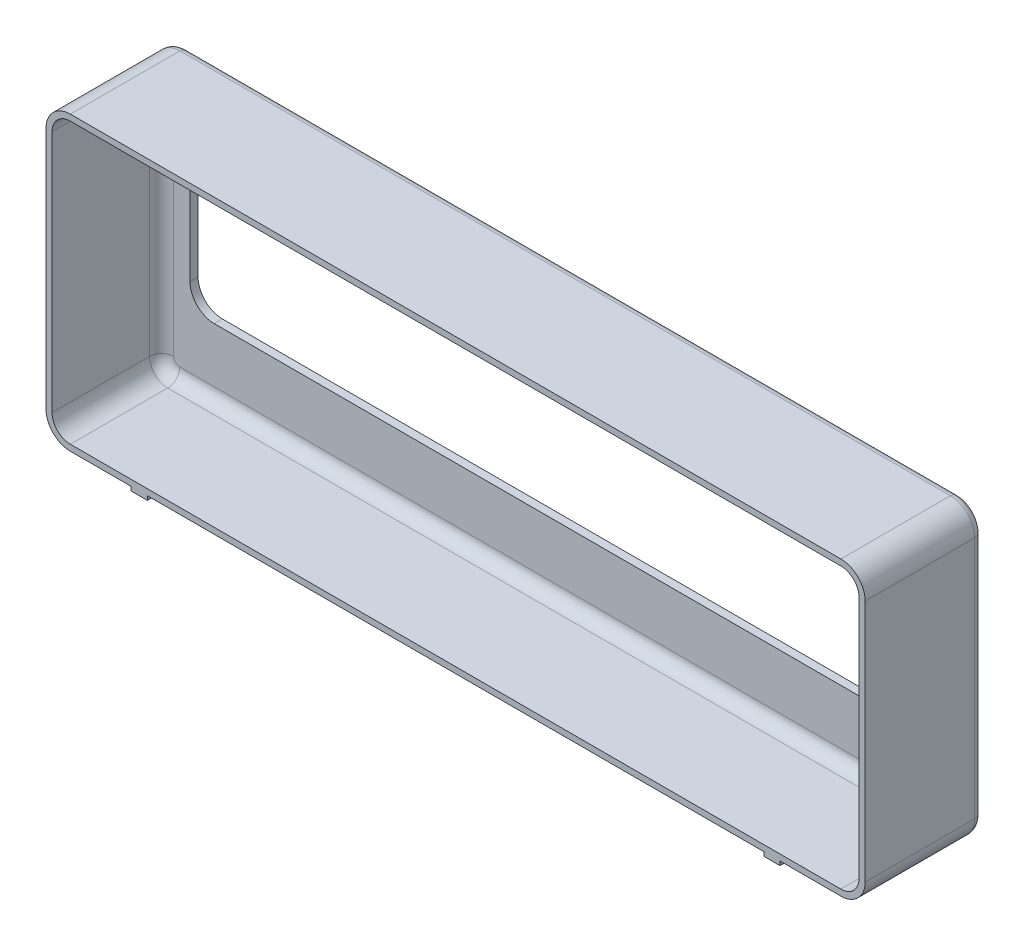
SolidWorks part; units mm, degrees
ref_plane "Front Plane" through (0, 0, 0) normal (0, 0, 1) x (1, 0, 0)
ref_plane "Top Plane" through (0, 0, 0) normal (0, 1, 0) x (1, 0, 0)
ref_plane "Right Plane" through (0, 0, 0) normal (1, 0, 0) x (0, 0, -1)
sketch "Sketch1" plane through (0, 0, 0) normal (0, 0, 1) x (1, 0, 0)
  line L1 (0, 0) -> (202, 0)
  line L2 (0, 0) -> (0, 72)
  line L3 (0, 72) -> (202, 72)
  line L4 (202, 0) -> (202, 72)
  dimension "D1" = 72
  dimension "D2" = 202
extrude "Boss-Extrude1" add sketch "Sketch1" along normal blind 29
sketch "Sketch2" plane through (0, 0, 29) normal (0, 0, 1) x (1, 0, 0)
  line L0 (202, 72) -> (0, 72) construction
  line L1 (1.5, 70.5) -> (200.5, 70.5)
  line L2 (1.5, 70.5) -> (1.5, 1.5)
  line L3 (1.5, 1.5) -> (200.5, 1.5)
  line L4 (200.5, 70.5) -> (200.5, 1.5)
  line L5 (0, 72) -> (0, 0) construction
  line L6 (0, 0) -> (202, 0) construction
  line L7 (202, 0) -> (202, 72) construction
  dimension "D1" = 1.5
  dimension "D2" = 1.5
  dimension "D3" = 1.5
  dimension "D4" = 1.5
extrude "Cut-Extrude1" cut sketch "Sketch2" against normal blind 27
sketch "Sketch3" plane through (0, 0, 2) normal (0, 0, 1) x (1, 0, 0)
  line L0 (200.5, 70.5) -> (1.5, 70.5) construction
  line L1 (8.5, 55) -> (193.5, 55)
  line L2 (8.5, 55) -> (8.5, 18)
  line L3 (8.5, 18) -> (193.5, 18)
  line L4 (193.5, 55) -> (193.5, 18)
  line L5 (1.5, 1.5) -> (200.5, 1.5) construction
  line L6 (1.5, 70.5) -> (1.5, 1.5) construction
  line L7 (200.5, 1.5) -> (200.5, 70.5) construction
  dimension "D1" = 15.5
  dimension "D2" = 16.5
  dimension "D3" = 7
  dimension "D4" = 7
extrude "Cut-Extrude2" cut sketch "Sketch3" against normal blind 27
fillet "Fillet1" radius 6 4 edges at (193.5, 18, 1) (193.5, 55, 1) (8.5, 18, 1) (8.5, 55, 1)
fillet "Fillet2" radius 4.5 4 edges at (200.5, 70.5, 15.5) (200.5, 1.5, 15.5) (1.5, 1.5, 15.5) (1.5, 70.5, 15.5)
fillet "Fillet3" radius 6 4 edges at (202, 0, 14.5) (202, 72, 14.5) (0, 0, 14.5) (0, 72, 14.5)
sketch "Sketch4" plane through (0, 0, 0) normal (0, -1, 0) x (-1, 0, 0)
  line L0 (-6, -29) -> (-196, -29) construction
  line L1 (-21, -29) -> (-25, -29)
  line L2 (-21, -29) -> (-21, 0)
  line L3 (-21, 0) -> (-25, 0)
  line L4 (-25, -29) -> (-25, 0)
  line L5 (-6, 0) -> (-196, 0) construction
  line L6 (-181, -29) -> (-177, -29)
  line L7 (-181, -29) -> (-181, 0)
  line L8 (-181, 0) -> (-177, 0)
  line L9 (-177, -29) -> (-177, 0)
  line L10 (-6, -29) -> (-6, 0) construction
  line L11 (-196, 0) -> (-196, -29) construction
  dimension "D1" = 15
  dimension "D2" = 4
  dimension "D3" = 4
  dimension "D4" = 15
extrude "Boss-Extrude2" add sketch "Sketch4" along normal blind 1
fillet "Fillet4" radius 2 9 edges at (188.5, 0, 0) (200.2426, 1.7574, 0) (202, 36, 0) (200.2426, 70.2426, 0) (13.5, 0, 0) (1.7574, 1.7574, 0) (0, 36, 0) (1.7574, 70.2426, 0) (101, 72, 0)
fillet "Fillet5" radius 3 8 edges at (199.182, 69.182, 2) (200.5, 36, 2) (199.182, 2.818, 2) (101, 1.5, 2) (2.818, 2.818, 2) (1.5, 36, 2) (2.818, 69.182, 2) (101, 70.5, 2)
